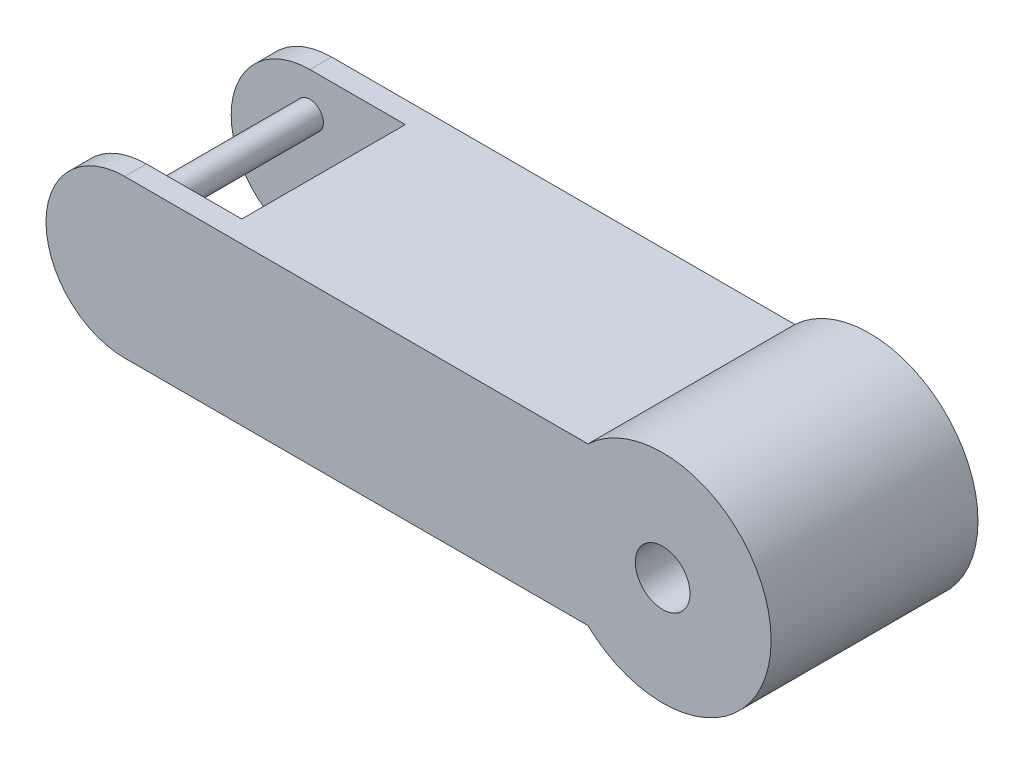
SolidWorks part; units mm, degrees
ref_plane "Front Plane" through (0, 0, 0) normal (0, 0, 1) x (1, 0, 0)
ref_plane "Top Plane" through (0, 0, 0) normal (0, 1, 0) x (1, 0, 0)
ref_plane "Right Plane" through (0, 0, 0) normal (1, 0, 0) x (0, 0, -1)
sketch "Sketch1" plane through (0, 0, 0) normal (0, 0, 1) x (1, 0, 0)
  line L1 (-13.7697, -14.5051) -> (-99.2033, -14.5051)
  line L3 (-13.7697, 14.5051) -> (-99.2033, 14.5051)
  line L5 (-94.0629, 13.5637) -> (-99.2033, 14.5051) construction
  line L6 (-94.0629, -13.5637) -> (-99.2033, -14.5051) construction
  circle A0 centre (0, 0) radius 20
  circle A1 centre (-99.2033, 0) radius 14.5051
  point P3 (-20, 0)
extrude "Boss-Extrude1" add sketch "Sketch1" along normal blind 4 contours A0 | A1 L1 A0 L3 | A1
sketch "Sketch2" plane through (0, 0, 4) normal (0, 0, 1) x (1, 0, 0)
  line L0 (-13.7697, 14.5051) -> (-99.2033, 14.5051) construction
  line L1 (-13.7697, -14.5051) -> (-99.2033, -14.5051) construction
  line L4 (-13.7697, 14.5051) -> (-99.2033, 14.5051)
  line L5 (-99.2033, -14.5051) -> (-13.7697, -14.5051)
  line L6 (-13.7697, 14.5051) -> (-83.4025, 14.5051)
  line L7 (-81.6041, -14.5051) -> (-13.7697, -14.5051)
  arc A0 (-83.4025, 14.5051) -> (-81.6041, -14.5051) centre (-82.5033, 0) cw
  arc A3 (-13.7697, -14.5051) -> (-13.7697, 14.5051) centre (0, 0) ccw
  arc A4 (-99.2033, 14.5051) -> (-99.2033, -14.5051) centre (-99.2033, 0) ccw
  arc A5 (-13.7697, -14.5051) -> (-13.7697, 14.5051) centre (0, 0) ccw
  arc M5 (-13.7697, -14.5051) -> (-13.7697, 14.5051) centre (0, 0) ccw
  line M6 (-13.7697, 14.5051) -> (-99.2033, 14.5051)
  line M8 (-99.2033, -14.5051) -> (-13.7697, -14.5051)
  dimension "D1" = 0
extrude "Boss-Extrude2" add sketch "Sketch2" along normal blind 15.075 contours A0 M6 M8 M5
mirror "Mirror1" about plane through (0, 0, 19.075) normal (0, 0, 1) of bodies 102
sketch "Sketch3" plane through (0, 0, 0) normal (0, 0, -1) x (-1, 0, 0)
  circle A0 centre (0, 0) radius 5.05
extrude "Cut-Extrude1" cut sketch "Sketch3" against normal blind 51.075
sketch "Sketch4" plane through (0, 0, 34.15) normal (0, 0, -1) x (-1, 0, 0)
  circle A1 centre (99.2033, 7.2525) radius 2.5
  circle A2 centre (99.2033, -7.2525) radius 2.5
extrude "Boss-Extrude3" add sketch "Sketch4" along normal blind 32 and the other way blind 2
